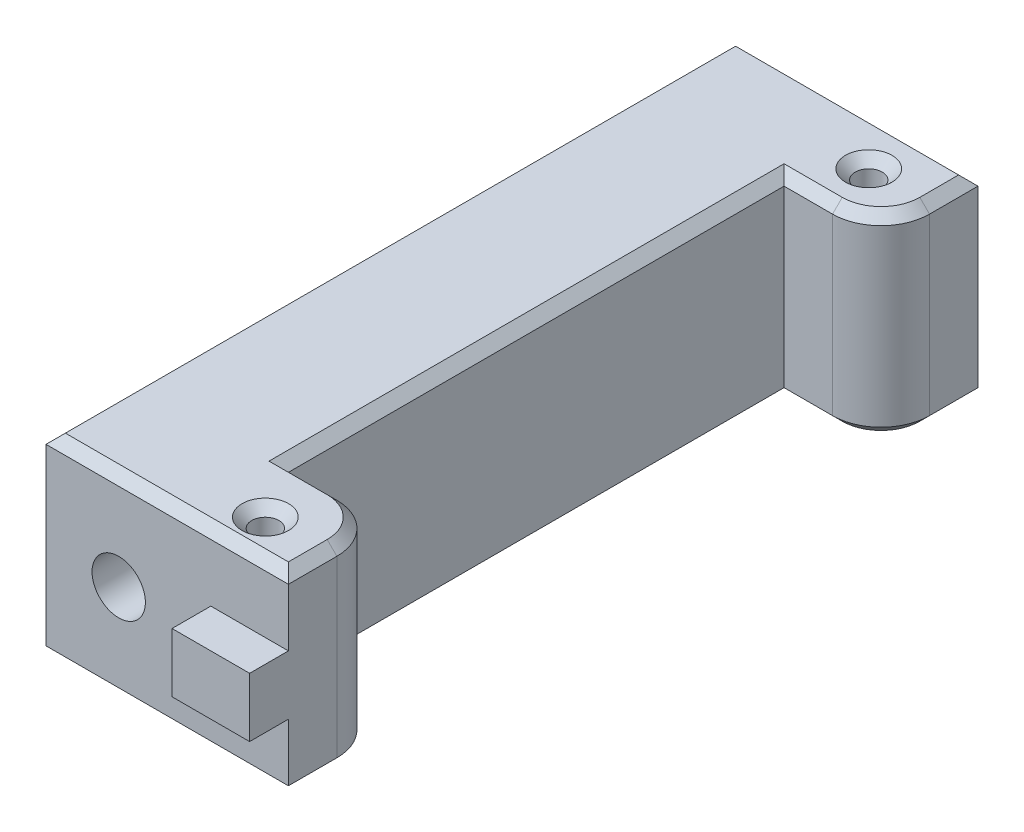
SolidWorks part; units mm, degrees
ref_plane "Front Plane" through (0, 0, 0) normal (0, 0, 1) x (1, 0, 0)
ref_plane "Top Plane" through (0, 0, 0) normal (0, 1, 0) x (1, 0, 0)
ref_plane "Right Plane" through (0, 0, 0) normal (1, 0, 0) x (0, 0, -1)
sketch "Sketch1" plane through (0, 0, 0) normal (0, 1, 0) x (1, 0, 0)
  line L0 (0, 0) -> (0, 71.12)
  line L2 (15, 61.12) -> (15, 10)
  line L3 (15, 10) -> (25, 10)
  line L4 (25, 10) -> (25, 0)
  line L5 (25, 0) -> (0, 0)
  line L6 (0, 71.12) -> (25, 71.12)
  line L7 (25, 71.12) -> (25, 61.12)
  line L8 (25, 61.12) -> (15, 61.12)
  point P10 (0, 0)
  point P11 (2.9264, 81.12)
  point P12 (0, 0)
  dimension "D1" = 25
  dimension "D2" = 15
  dimension "D3" = 10
  dimension "D4" = 71.12
  dimension "D5" = 10
extrude "Boss-Extrude1" add sketch "Sketch1" along normal blind 20
sketch "Sketch2" plane through (0, 0, -71.12) normal (0, 0, -1) x (-1, 0, 0)
  line L0 (0, 10) -> (-25, 10) construction
  line L1 (0, 20) -> (0, 0) construction
  line L2 (-25, 20) -> (-25, 0) construction
  point P6 (-7.5, 10)
  dimension "D1" = 7.5
hole_wizard "CBORE for M5 SHCS1" positions "Sketch3" profile "Sketch4" counterbore size "M5" standard "ANSI Metric" end condition through all
sketch "Sketch3" plane through (0, 0, -71.12) normal (0, 0, -1) x (-1, 0, 0)
  point P0 (-7.5, 10)
sketch "Sketch4" plane through (7.5, 10, -71.12) normal (1, 0, 0) x (0, 1, 0)
  line L0 (0, 0) -> (0, 71.12)
  line L1 (0, 71.12) -> (2.75, 71.12)
  line L3 (2.75, 71.12) -> (2.75, 65)
  line L4 (2.75, 65) -> (5, 65)
  line L5 (5, 65) -> (5, 0)
  line L7 (5, 0) -> (0, 0)
  line L11 (0, -6.35) -> (0, 107.95) construction
  dimension "Thru Hole Dia." = 5.5
  dimension "Thru Hole Depth" = 71.12
  dimension "C'Bore Dia." = 10
  dimension "C'Bore Depth" = 65
sketch "Sketch5" plane through (0, 0, 0) normal (0, 0, 1) x (1, 0, 0)
  line L0 (25, 10) -> (10.25, 10) construction
  line L1 (25, 20) -> (25, 0) construction
  line L3 (17, 6.95) -> (25, 6.95)
  line L4 (17, 6.95) -> (17, 13.05)
  line L5 (17, 13.05) -> (25, 13.05)
  line L6 (25, 6.95) -> (25, 13.05)
  line L7 (17, 6.95) -> (25, 13.05) construction
  line L8 (17, 13.05) -> (25, 6.95) construction
  circle A0 centre (7.5, 10) radius 2.75 construction
  point P7 (21, 10)
  dimension "D1" = 6.1
  dimension "D2" = 8
extrude "Boss-Extrude2" add sketch "Sketch5" along normal blind 4
sketch "Sketch6" plane through (0, 0, 0) normal (0, -1, 0) x (1, 0, 0)
  line L0 (15, -10) -> (15, -61.12) construction
  line L1 (0, 0) -> (25, 0) construction
  circle A0 centre (18.81, -3.81) radius 1.4
  circle A1 centre (18.81, -66.04) radius 1.4
  point P8 (0, 0)
  point P9 (18.81, -3.81)
  point P10 (18.81, -64.7025)
  dimension "D3" = 2.8
  dimension "D1" = 3.81
  dimension "D2" = 3.81
  dimension "D4" = 62.23
extrude "Cut-Extrude1" cut sketch "Sketch6" against normal through all
fillet "Fillet1" radius 5 2 edges at (25, 10, -10) (25, 10, -61.12)
chamfer "Chamfer2" distance 1 angle 45 24 edges at (12.5, 20, 0) (0, 20, -35.56) (12.5, 20, -71.12) (25, 20, -68.62) (23.5355, 20, -62.5845) (17.5, 20, -61.12) (15, 20, -35.56) (17.5, 20, -10) (23.5355, 20, -8.5355) (25, 20, -2.5) (18.81, 20, -67.44) (18.81, 20, -5.21) (15, 0, -35.56) (17.5, 0, -61.12) (23.5355, 0, -62.5845) (25, 0, -68.62) (12.5, 0, -71.12) (0, 0, -35.56) (12.5, 0, 0) (25, 0, -2.5) (23.5355, 0, -8.5355) (17.5, 0, -10) (18.81, 0, -67.44) (18.81, 0, -5.21)
